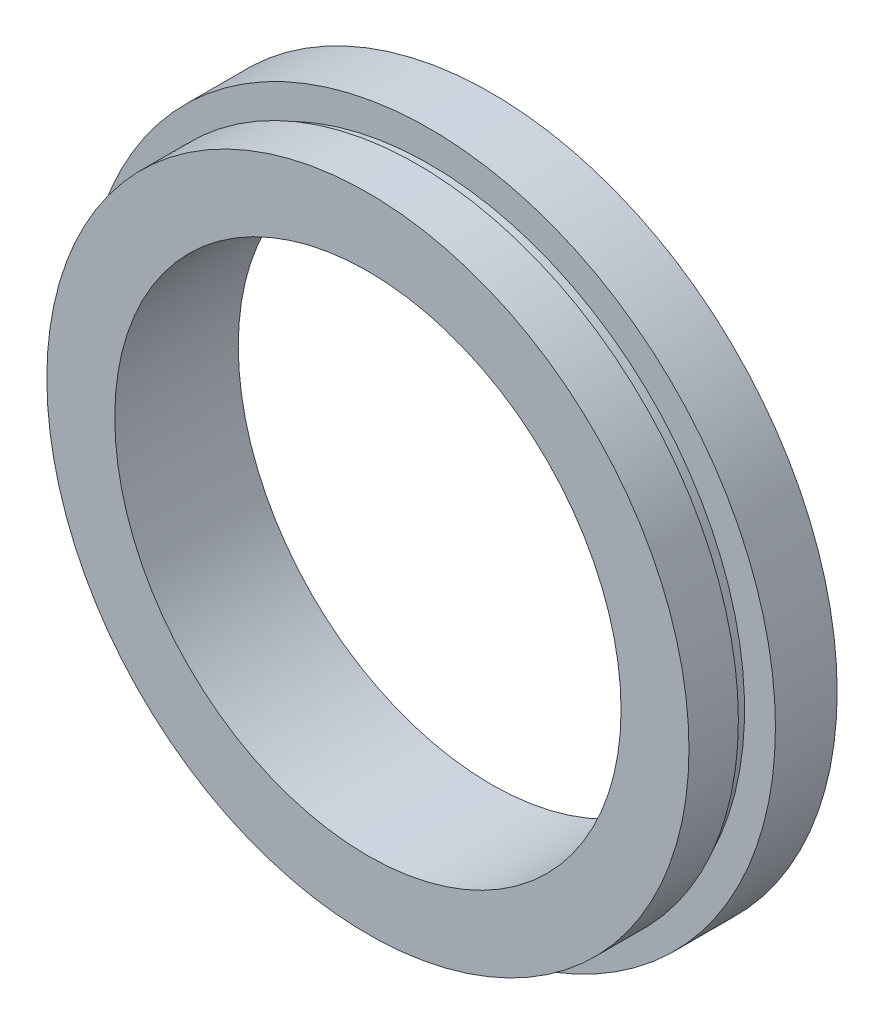
SolidWorks part; units mm, degrees
ref_plane "前视基准面" through (0, 0, 0) normal (0, 0, 1) x (1, 0, 0)
ref_plane "上视基准面" through (0, 0, 0) normal (0, 1, 0) x (1, 0, 0)
ref_plane "右视基准面" through (0, 0, 0) normal (1, 0, 0) x (0, 0, -1)
sketch "草图1" plane through (0, 0, 0) normal (0, 1, 0) x (1, 0, 0)
  line L0 (0, 19.1406) -> (0, -28.4043) construction
  line L1 (20.5, 0) -> (20.5, 10)
  line L2 (20.5, 0) -> (26, 0)
  line L3 (26, 0) -> (26, 4)
  line L4 (26, 4) -> (25.5, 4)
  line L5 (25.5, 4) -> (25.5, 5)
  line L6 (25.5, 5) -> (28, 5)
  line L7 (28, 5) -> (28, 10)
  line L8 (28, 10) -> (20.5, 10)
  dimension "D3" = 25.5
  dimension "D1" = 20.5
  dimension "D2" = 26
  dimension "D4" = 28
  dimension "D5" = 1
  dimension "D6" = 5
  dimension "D7" = 10
revolve "旋转1" add sketch "草图1" angle 360 about L0
cosmetic thread "装饰螺纹线1" parameters "D2"=42
cosmetic thread "装饰螺纹线2" parameters "D2"=51
